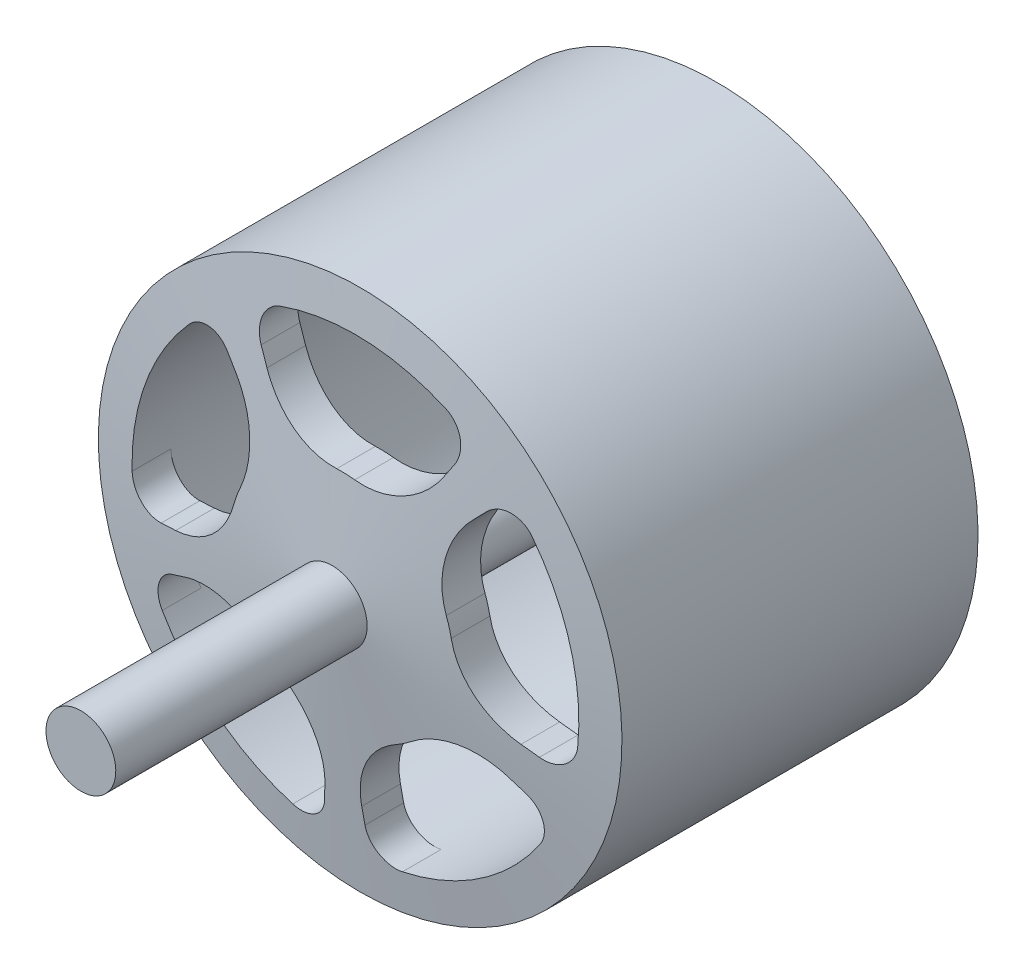
SolidWorks part; units mm, degrees
material "AISI 1020 Steel, Cold Rolled"
ref_plane "Front Plane" through (0, 0, 0) normal (0, 0, 1) x (1, 0, 0)
ref_plane "Top Plane" through (0, 0, 0) normal (0, 1, 0) x (1, 0, 0)
ref_plane "Right Plane" through (0, 0, 0) normal (1, 0, 0) x (0, 0, -1)
sketch "Sketch1" plane through (0, 0, 0) normal (1, 0, 0) x (0, 0, -1)
  line L0 (0, 0) -> (-45.5, 0) construction
  line L1 (-45.5, 0) -> (-45.5, 2.5)
  line L2 (-45.5, 2.5) -> (-27.5, 2.5)
  line L3 (-27.5, 2.5) -> (-25.5, 18.75)
  line L4 (-25.5, 18.75) -> (0, 18.75)
  line L5 (0, 18.75) -> (0, 0) construction
  line L6 (-45.5, 0) -> (0, 0)
  line L8 (-23.0677, 16) -> (0, 16)
  line L9 (0, 16) -> (0, 18.75)
  line L10 (-27.5, 2.5) -> (-24.7706, 2.1641) construction
  line L12 (7.7, 2.5) -> (-24.7292, 2.5)
  line L13 (-23.0677, 16) -> (-24.7706, 2.1641) construction
  line L14 (-23.0677, 16) -> (-24.7292, 2.5)
  line L15 (7.7, 2.5) -> (7.7, 0)
  line L16 (7.7, 0) -> (0, 0)
  dimension "D1" = 18.75
  dimension "D2" = 2.5
  dimension "D3" = 18
  dimension "D4" = 45.5
  dimension "D5" = 20
  dimension "D6" = 16
  dimension "D7" = 53.2
revolve "Revolve1" add sketch "Sketch1" angle 360 about L6
sketch "Sketch2" plane through (0, 0, 0) normal (0, 0, 1) x (1, 0, 0)
  line L0 (0, 0) -> (8.497, 13.5573) construction
  line L1 (0, 0) -> (-7.4924, 14.1373) construction
  line L2 (-6.4886, 12.2433) -> (-5.9233, 11.1765)
  line L3 (7.3587, 11.741) -> (6.7175, 10.718)
  circle A0 centre (0, 0) radius 16 construction
  arc A1 (-5.396, 15.0627) -> (6.4731, 14.6321) centre (0, 0) cw
  circle A2 centre (0, 0) radius 8 construction
  arc A3 (-0.3553, 7.9921) -> (0.9334, 7.9454) centre (0, 0) cw
  arc A4 (6.4731, 14.6321) -> (7.3587, 11.741) centre (5.664, 12.8031) cw
  arc A5 (-6.4886, 12.2433) -> (-5.396, 15.0627) centre (-4.7215, 13.1798) cw
  arc A6 (0.9334, 7.9454) -> (6.7175, 10.718) centre (1.6335, 13.9044) ccw
  arc A7 (-0.3553, 7.9921) -> (-5.9233, 11.1765) centre (-0.6218, 13.9862) cw
  point P18 (4.2485, 6.7786)
  point P21 (-3.7462, 7.0687)
  dimension "D1" = 32
  dimension "D3" = 16
  dimension "D4" = 2
  dimension "D5" = 6
  dimension "D2" = 60
extrude "Cut-Extrude1" cut sketch "Sketch2" along normal through all contours A3 A6 L3 A4 A1 A5 L2 A7
pattern_circular "CirPattern1" count 5 over 360 about axis through (0, 0, 0) along (0, 0, 1) of "Cut-Extrude1"
